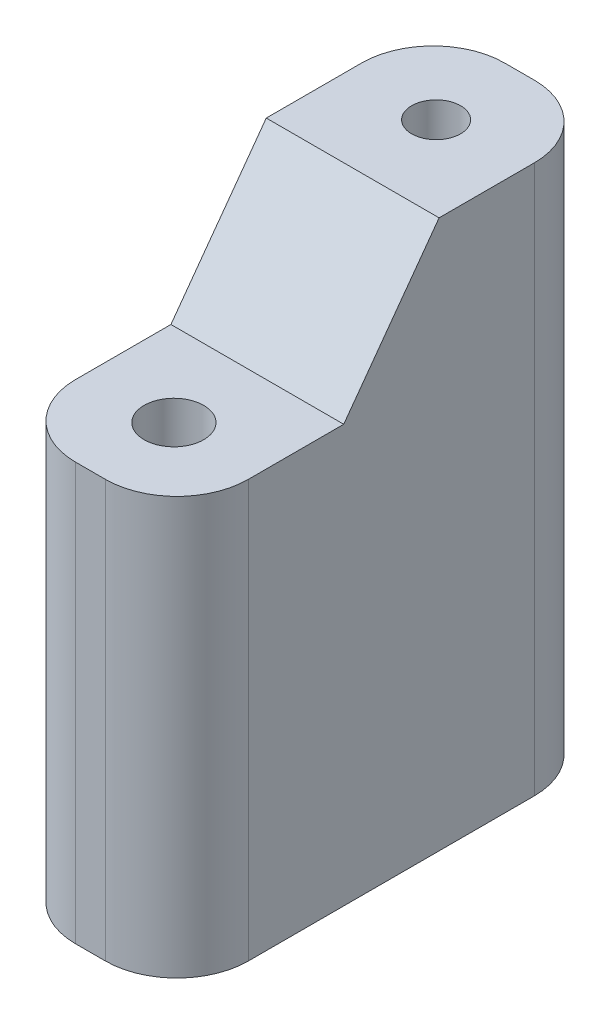
SolidWorks part; units mm, degrees
material "Delrin 2700 NC010, Low Viscosity Acetal Copolymer (SS)"
ref_plane "Front Plane" through (0, 0, 0) normal (0, 0, 1) x (1, 0, 0)
ref_plane "Top Plane" through (0, 0, 0) normal (0, 1, 0) x (1, 0, 0)
ref_plane "Right Plane" through (0, 0, 0) normal (1, 0, 0) x (0, 0, -1)
sketch "Sketch1" plane through (0, 0, 0) normal (0, 1, 0) x (1, 0, 0)
  line L1 (-3.625, -9) -> (3.625, -9)
  line L2 (-3.625, -9) -> (-3.625, 9)
  line L3 (-3.625, 9) -> (3.625, 9)
  line L4 (3.625, -9) -> (3.625, 9)
  line L5 (-3.625, -9) -> (3.625, 9) construction
  line L6 (-3.625, 9) -> (3.625, -9) construction
  point P0 (0, 0)
  dimension "D1" = 7.25
  dimension "D2" = 18
extrude "Boss-Extrude1" add sketch "Sketch1" along normal blind 23
sketch "Sketch2" plane through (-3.625, 0, 0) normal (-1, 0, 0) x (0, 0, 1)
  line L0 (-2, 23) -> (2, 17.5)
  line L1 (-9, 23) -> (9, 23) construction
  line L2 (2, 17.5) -> (9, 17.5)
  line L3 (9, 23) -> (9, 0) construction
  line L4 (-9, 0) -> (9, 0) construction
  line L5 (-2, 23) -> (-9, 23)
  dimension "D1" = 17.5
  dimension "D2" = 7
  dimension "D3" = 7
extrude "Cut-Extrude1" cut sketch "Sketch2" against normal through all and the other way through all flip side to cut
hole_wizard "M2.5x0.45 Tapped Hole1" positions "Sketch4" profile "Sketch3" tap size "M2.5x0.45" standard "ANSI Metric"
sketch "Sketch4" plane through (0, 0, 0) normal (0, -1, 0) x (-1, 0, 0)
  point P0 (0, 0)
sketch "Sketch3" plane through (0, 0, 0) normal (1, 0, 0) x (0, 0, -1)
  line L0 (0, 0) -> (0, 6.9659)
  line L1 (0, 6.9659) -> (1.025, 6.35)
  line L2 (1.025, 6.35) -> (1.025, 0)
  line L5 (1.025, 0) -> (0, 0)
  line L10 (0, 6.9659) -> (-1.025, 6.35) construction
  line L11 (0, -6.35) -> (0, 107.95) construction
  dimension "Tap Drill Dia." = 2.05
  dimension "Tap Drill Depth" = 6.35
  dimension "Drill Angle" = 118
cosmetic thread "Hole Thread1" parameters "D1"=5, "D2"=2.5
hole_wizard "M2.5x0.45 Tapped Hole2" positions "Sketch6" profile "Sketch5" tap size "M2.5x0.45" standard "ANSI Metric"
sketch "Sketch6" plane through (0, 23, 0) normal (0, 1, 0) x (1, 0, 0)
  line L0 (0, 9) -> (0, 2) construction
  line L1 (3.625, 9) -> (-3.625, 9) construction
  line L2 (-3.625, 2) -> (3.625, 2) construction
  point P0 (0, 5.5)
sketch "Sketch5" plane through (0, 23, -5.5) normal (1, 0, 0) x (0, 0, 1)
  line L0 (0, 0) -> (0, 6.9659)
  line L1 (0, 6.9659) -> (1.025, 6.35)
  line L2 (1.025, 6.35) -> (1.025, 0)
  line L5 (1.025, 0) -> (0, 0)
  line L10 (0, 6.9659) -> (-1.025, 6.35) construction
  line L11 (0, -6.35) -> (0, 107.95) construction
  dimension "Tap Drill Dia." = 2.05
  dimension "Tap Drill Depth" = 6.35
  dimension "Drill Angle" = 118
cosmetic thread "Hole Thread2" parameters "D1"=5, "D2"=2.5
hole_wizard "M2.5x0.45 Tapped Hole3" positions "Sketch8" profile "Sketch7" tap size "M2.5x0.45" standard "ANSI Metric"
sketch "Sketch8" plane through (0, 17.5, 0) normal (0, 1, 0) x (1, 0, 0)
  line L0 (0, -2) -> (0, -9) construction
  line L1 (-3.625, -2) -> (3.625, -2) construction
  line L2 (3.625, -9) -> (-3.625, -9) construction
  point P0 (0, -5.5)
sketch "Sketch7" plane through (0, 17.5, 5.5) normal (1, 0, 0) x (0, 0, 1)
  line L0 (0, 0) -> (0, 6.9659)
  line L1 (0, 6.9659) -> (1.025, 6.35)
  line L2 (1.025, 6.35) -> (1.025, 5)
  line L3 (1.025, 5) -> (1.25, 5)
  line L4 (1.25, 5) -> (1.25, 0)
  line L5 (1.25, 0) -> (0, 0)
  line L10 (0, 6.9659) -> (-1.025, 6.35) construction
  line L11 (0, -6.35) -> (0, 107.95) construction
  dimension "Tap Drill Dia." = 2.05
  dimension "Tap Drill Depth" = 6.35
  dimension "Thread Major Dia." = 2.5
  dimension "Thread Depth" = 5
  dimension "Drill Angle" = 118
fillet "Fillet1" radius 3 4 edges at (3.625, 8.75, 9) (-3.625, 8.75, 9) (3.625, 11.5, -9) (-3.625, 11.5, -9)
